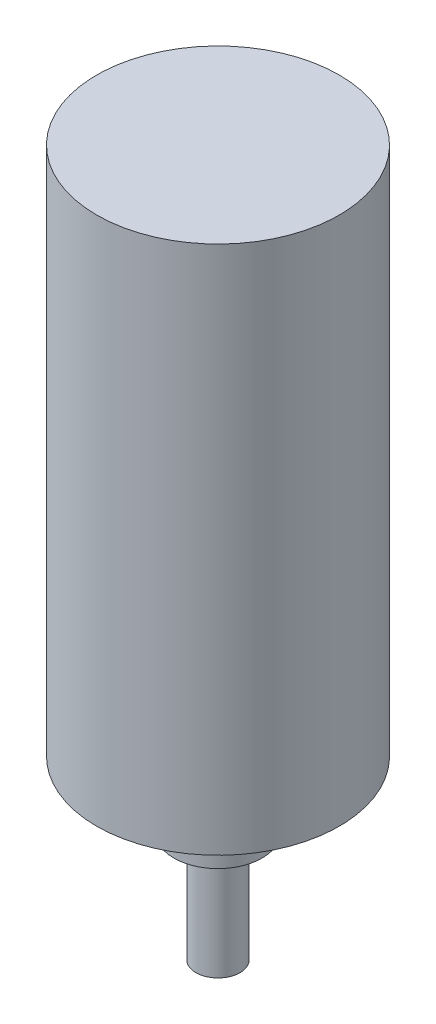
SolidWorks part; units mm, degrees
ref_plane "Front Plane" through (0, 0, 0) normal (0, 0, 1) x (1, 0, 0)
ref_plane "Top Plane" through (0, 0, 0) normal (0, 1, 0) x (1, 0, 0)
ref_plane "Right Plane" through (0, 0, 0) normal (1, 0, 0) x (0, 0, -1)
sketch "Sketch1" plane through (0, 0, 0) normal (0, 1, 0) x (1, 0, 0)
  line L0 (-1.5, 1.3229) -> (1.5, 1.3229)
  arc A0 (-1.5, 1.3229) -> (1.5, 1.3229) centre (0, 0) ccw
  dimension "D1" = 4
  dimension "D2" = 3
extrude "Boss-Extrude1" add sketch "Sketch1" along normal blind 8
sketch "Sketch2" plane through (0, 8, 0) normal (0, 1, 0) x (1, 0, 0)
  circle A0 centre (0, 0) radius 2
  dimension "D1" = 4
extrude "Boss-Extrude2" add sketch "Sketch2" along normal blind 2
sketch "Sketch3" plane through (0, 10, 0) normal (0, 1, 0) x (1, 0, 0)
  circle A0 centre (0, 0) radius 4
  dimension "D1" = 8
extrude "Boss-Extrude3" add sketch "Sketch3" along normal blind 6
sketch "Sketch4" plane through (0, 16, 0) normal (0, 1, 0) x (1, 0, 0)
  circle A0 centre (0, 0) radius 11
  dimension "D1" = 22
extrude "Boss-Extrude4" add sketch "Sketch4" along normal blind 48
